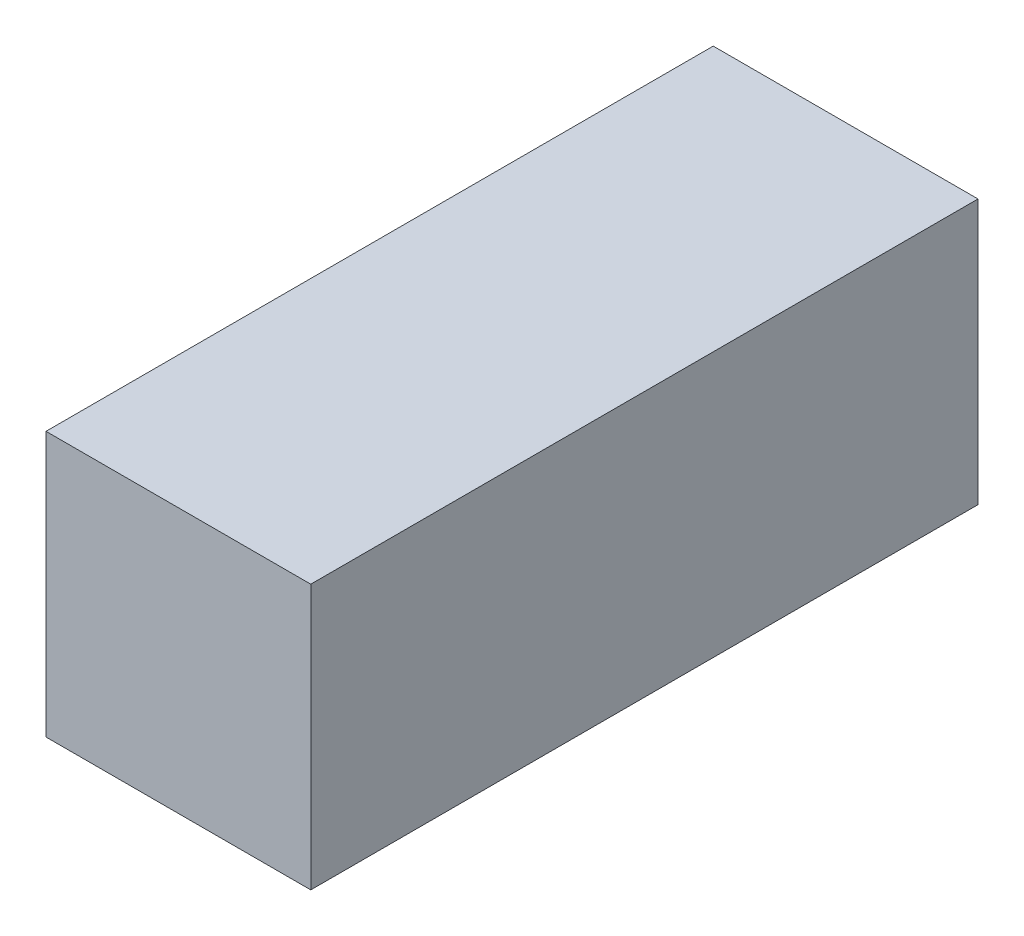
SolidWorks part; units mm, degrees
material "PF"
ref_plane "Front Plane" through (0, 0, 0) normal (0, 0, 1) x (1, 0, 0)
ref_plane "Top Plane" through (0, 0, 0) normal (0, 1, 0) x (1, 0, 0)
ref_plane "Right Plane" through (0, 0, 0) normal (1, 0, 0) x (0, 0, -1)
sketch "Sketch1" plane through (0, 0, 0) normal (0, 0, 1) x (1, 0, 0)
  line L1 (0, 0) -> (25, 0)
  line L2 (0, 0) -> (0, -25)
  line L3 (0, -25) -> (25, -25)
  line L4 (25, 0) -> (25, -25)
  dimension "D1" = 25
extrude "Boss-Extrude1" add sketch "Sketch1" along normal blind 63
